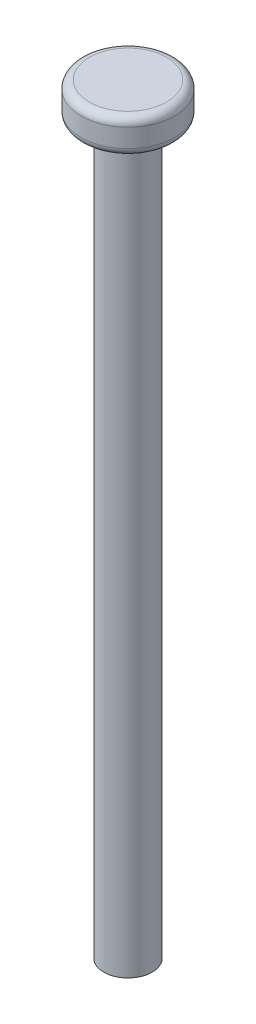
SolidWorks part; units mm, degrees
ref_plane "Спереди" through (0, 0, 0) normal (0, 0, 1) x (1, 0, 0)
ref_plane "Сверху" through (0, 0, 0) normal (0, 1, 0) x (1, 0, 0)
ref_plane "Справа" through (0, 0, 0) normal (1, 0, 0) x (0, 0, -1)
sketch "Sketch1" plane through (0, 0, 0) normal (0, 1, 0) x (1, 0, 0)
  circle A0 centre (0, 0) radius 3
  dimension "D1" = 6
extrude "Boss-Extrude1" add sketch "Sketch1" along normal blind 90
sketch "Sketch2" plane through (0, 90, 0) normal (0, 1, 0) x (1, 0, 0)
  circle A0 centre (0, 0) radius 5.8
  dimension "D1" = 11.6
extrude "Boss-Extrude2" add sketch "Sketch2" along normal blind 4.3
fillet "Fillet1" radius 1 2 edges at (0, 90, 5.8) (0, 94.3, 5.8)
